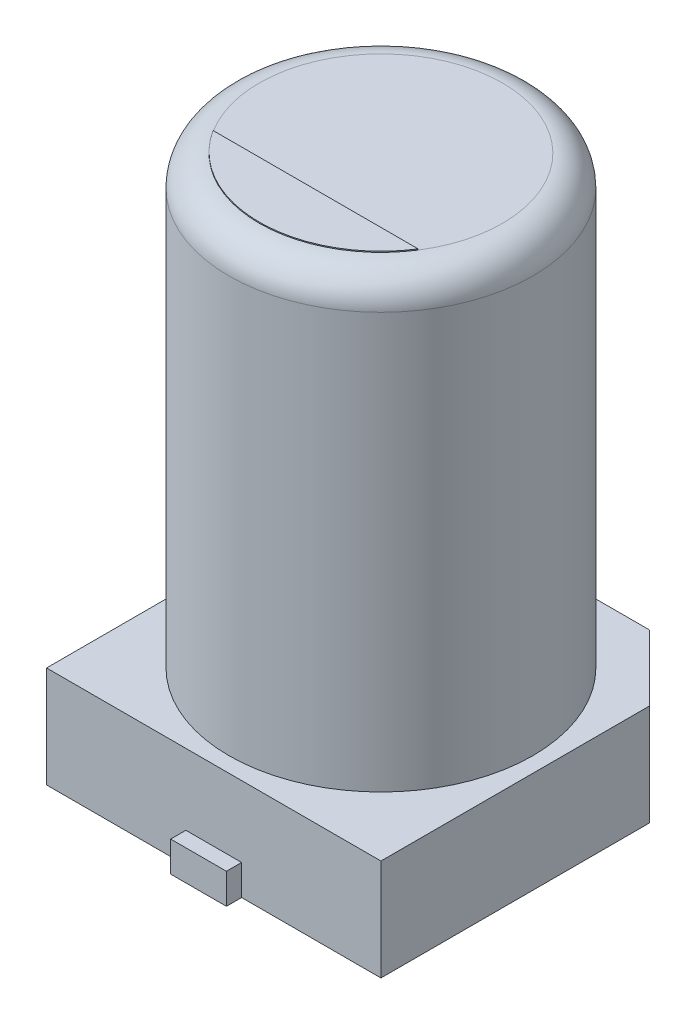
SolidWorks part; units mm, degrees
ref_plane "Front Plane" through (0, 0, 0) normal (0, 0, 1) x (1, 0, 0)
ref_plane "Top Plane" through (0, 0, 0) normal (0, 1, 0) x (1, 0, 0)
ref_plane "Right Plane" through (0, 0, 0) normal (1, 0, 0) x (0, 0, -1)
sketch "Sketch2" plane through (0, 0, 0) normal (0, 1, 0) x (1, 0, 0)
  line L0 (0, 0) -> (0, 2.085) construction
  line L1 (0, 0) -> (2.9643, 0) construction
  line L2 (1.65, -1.65) -> (-1.65, -1.65)
  line L3 (-1.65, -1.65) -> (-1.65, 1)
  line L4 (-1.65, 1) -> (-1, 1.65)
  line L5 (-1, 1.65) -> (1, 1.65)
  line L6 (1, 1.65) -> (1.65, 1)
  line L7 (1.65, 1) -> (1.65, -1.65)
  line L8 (0, -1.65) -> (0, -0.9795) construction
  line L9 (0, 1.65) -> (0, 2.1922) construction
  line L10 (-0.2934, -1.65) -> (-0.2934, 1.65) construction
  line L11 (-0.2934, 0) -> (-0.8682, 0) construction
  dimension "D1" = 3.3
  dimension "D2" = 3.3
  dimension "D3" = 2
extrude "Boss-Extrude1" add sketch "Sketch2" along normal blind 1
sketch "Sketch3" plane through (0, 0, 0) normal (0, 1, 0) x (1, 0, 0)
  circle A0 centre (0, 0) radius 1.5
  dimension "D1" = 3
extrude "Boss-Extrude2" add sketch "Sketch3" along normal blind 5.4 contours A0
fillet "Fillet1" radius 0.3 1 edges at (0, 5.4, 1.5)
sketch "Sketch4" plane through (0, 0, 0) normal (0, 1, 0) x (1, 0, 0)
  line L13 (0, 0) -> (0.593, 0) construction
  line L14 (0.275, 1.8) -> (-0.275, 1.8)
  line L15 (0.275, -0.3) -> (-0.275, -0.3)
  line L16 (0.275, -0.3) -> (0.275, -1.8)
  line L17 (0.275, -1.8) -> (-0.275, -1.8)
  line L18 (-0.275, -0.3) -> (-0.275, -1.8)
  line L19 (0.275, -0.3) -> (-0.275, -1.8) construction
  line L20 (0.275, -1.8) -> (-0.275, -0.3) construction
  line L21 (-0.275, 0.3) -> (-0.275, 1.8)
  line L22 (0.275, 0.3) -> (-0.275, 0.3)
  line L23 (0.275, 0.3) -> (0.275, 1.8)
  line L24 (0.275, 1.8) -> (-0.275, 0.3) construction
  line L25 (0.275, 0.3) -> (-0.275, 1.8) construction
  point P13 (0, -1.05)
  point P23 (0, 1.05)
  dimension "D4" = 0.55
  dimension "D5" = 1.5
  dimension "D6" = 0.6
extrude "Boss-Extrude3" add sketch "Sketch4" along normal blind 0.3
ref_plane "Plane1" through (0, 5.4, 0) normal (0, 1, 0) x (1, 0, 0)
sketch "Sketch5" plane through (0, 5.4, 0) normal (0, 1, 0) x (1, 0, 0)
  line L0 (1.012, -0.6449) -> (-1.012, -0.6449)
  circle A0 centre (0, 0) radius 1.2 construction
  arc A1 (1.012, -0.6449) -> (-1.012, -0.6449) centre (0, 0) cw
extrude "Boss-Extrude4" add sketch "Sketch5" along normal blind 0.01
